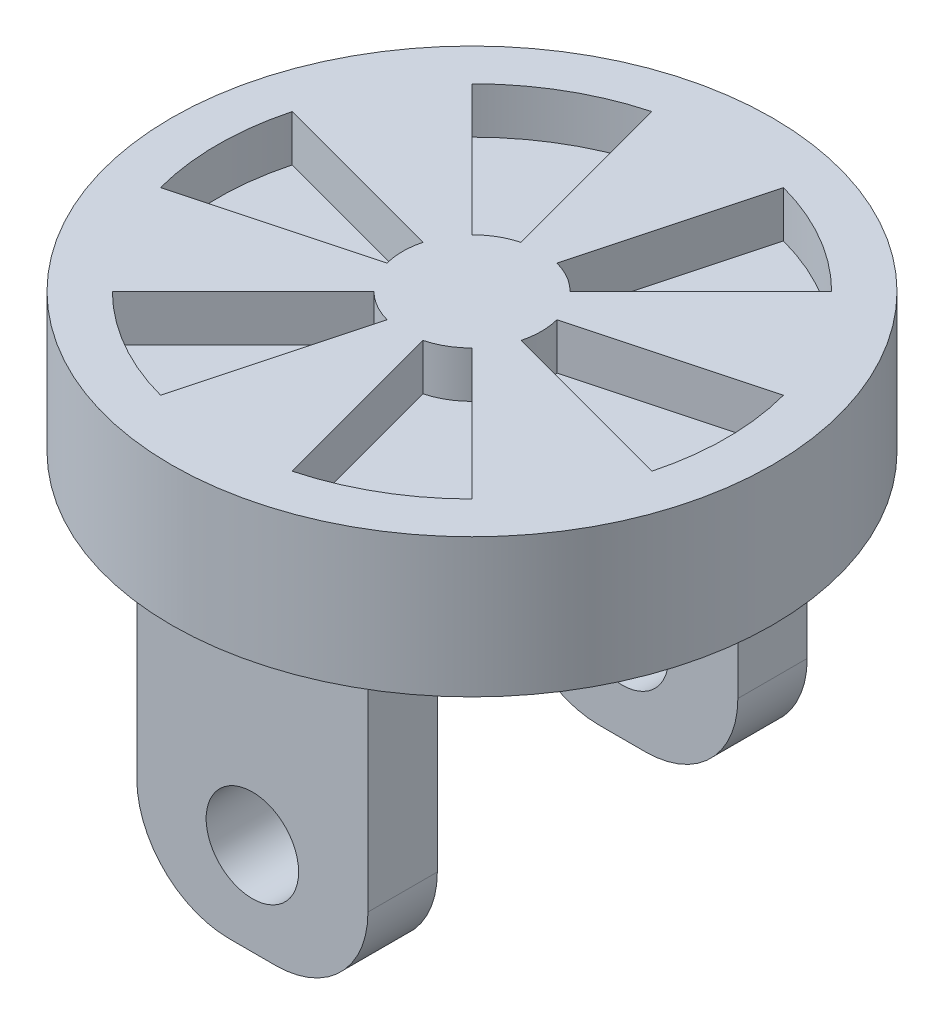
SolidWorks part; units mm, degrees
ref_plane "前视基准面" through (0, 0, 0) normal (0, 0, 1) x (1, 0, 0)
ref_plane "上视基准面" through (0, 0, 0) normal (0, 1, 0) x (1, 0, 0)
ref_plane "右视基准面" through (0, 0, 0) normal (1, 0, 0) x (0, 0, -1)
sketch "草图1" plane through (0, 0, 0) normal (0, 1, 0) x (1, 0, 0)
  circle A0 centre (0, 0) radius 65
  point P3 (-187.0694, 59.292)
extrude "凸台-拉伸1" add sketch "草图1" along normal blind 30
sketch "草图2" plane through (0, 0, 0) normal (0, -1, 0) x (1, 0, 0)
  line L0 (0, 65) -> (0, -65) construction
  line L1 (65, 0) -> (-65, 0) construction
  line L2 (-25, 47.5) -> (25, 47.5)
  line L3 (-25, 47.5) -> (-25, 32.5)
  line L4 (-25, 32.5) -> (25, 32.5)
  line L5 (25, 47.5) -> (25, 32.5)
  line L6 (-25, 47.5) -> (25, 32.5) construction
  line L7 (-25, 32.5) -> (25, 47.5) construction
  line L8 (-25, -32.5) -> (25, -32.5)
  line L9 (25, -47.5) -> (25, -32.5)
  line L10 (-25, -47.5) -> (25, -47.5)
  line L11 (-25, -47.5) -> (-25, -32.5)
  circle A0 centre (0, 0) radius 65 construction
  point P5 (0, 40)
  dimension "D1" = 50
  dimension "D2" = 15
  dimension "D3" = 40
extrude "凸台-拉伸2" add sketch "草图2" along normal blind 70
fillet "圆角2" radius 20 4 edges at (25, -70, 40) (25, -70, -40) (-25, -70, -40) (-25, -70, 40)
sketch "草图3" plane through (0, 0, 47.5) normal (0, 0, 1) x (1, 0, 0)
  line L0 (0, -70) -> (0, -50) construction
  line L1 (5, -70) -> (-5, -70) construction
  circle A1 centre (0, -50) radius 10
  dimension "D1" = 20
extrude "切除-拉伸1" cut sketch "草图3" against normal through all
sketch "草图7" plane through (0, 30, 0) normal (0, 1, 0) x (1, 0, 0)
  line L0 (55, 0) -> (15, 0) construction
  line L1 (14.4889, 3.8823) -> (53.1259, 14.235)
  line L2 (14.4889, -3.8823) -> (53.1259, -14.235)
  line L3 (10.6066, -10.6066) -> (38.8909, -38.8909)
  line L4 (3.8823, -14.4889) -> (14.235, -53.1259)
  line L5 (-3.8823, -14.4889) -> (-14.235, -53.1259)
  line L6 (-10.6066, -10.6066) -> (-38.8909, -38.8909)
  line L7 (-14.4889, -3.8823) -> (-53.1259, -14.235)
  line L8 (-14.4889, 3.8823) -> (-53.1259, 14.235)
  line L9 (-10.6066, 10.6066) -> (-38.8909, 38.8909)
  line L10 (-3.8823, 14.4889) -> (-14.235, 53.1259)
  line L11 (3.8823, 14.4889) -> (14.235, 53.1259)
  line L12 (10.6066, 10.6066) -> (38.8909, 38.8909)
  arc A0 (14.4889, -3.8823) -> (14.4889, 3.8823) centre (0, 0) ccw
  arc A1 (53.1259, -14.235) -> (53.1259, 14.235) centre (0, 0) ccw
  arc A2 (14.235, -53.1259) -> (38.8909, -38.8909) centre (0, 0) ccw
  arc A3 (3.8823, -14.4889) -> (10.6066, -10.6066) centre (0, 0) ccw
  arc A4 (-38.8909, -38.8909) -> (-14.235, -53.1259) centre (0, 0) ccw
  arc A5 (-10.6066, -10.6066) -> (-3.8823, -14.4889) centre (0, 0) ccw
  arc A6 (-53.1259, 14.235) -> (-53.1259, -14.235) centre (0, 0) ccw
  arc A7 (-14.4889, 3.8823) -> (-14.4889, -3.8823) centre (0, 0) ccw
  arc A8 (-14.235, 53.1259) -> (-38.8909, 38.8909) centre (0, 0) ccw
  arc A9 (-3.8823, 14.4889) -> (-10.6066, 10.6066) centre (0, 0) ccw
  arc A10 (38.8909, 38.8909) -> (14.235, 53.1259) centre (0, 0) ccw
  arc A11 (10.6066, 10.6066) -> (3.8823, 14.4889) centre (0, 0) ccw
  point P30 (0, 0)
  dimension "D1" = 110
  dimension "D2" = 30
  dimension "D3" = 15
  dimension "D4" = 6
extrude "切除-拉伸2" cut sketch "草图7" against normal blind 10
